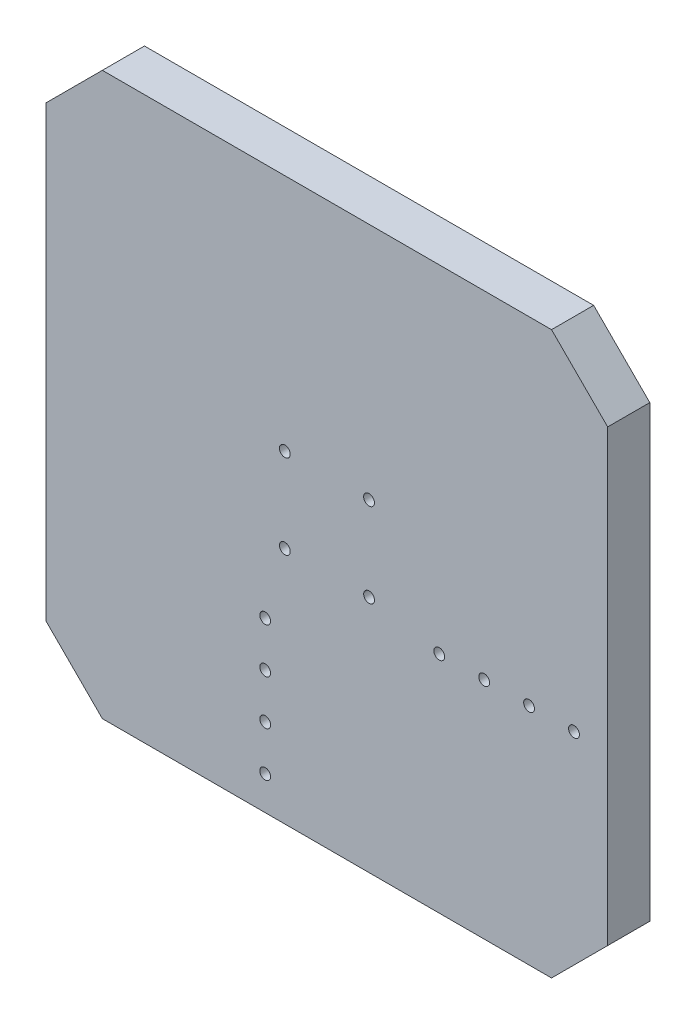
SolidWorks part; units mm, degrees
ref_plane "Front Plane" through (0, 0, 0) normal (0, 0, 1) x (1, 0, 0)
ref_plane "Top Plane" through (0, 0, 0) normal (0, 1, 0) x (1, 0, 0)
ref_plane "Right Plane" through (0, 0, 0) normal (1, 0, 0) x (0, 0, -1)
sketch "Sketch2" plane through (0, 0, 0) normal (0, 0, 1) x (1, 0, 0)
  line L1 (-100, -100) -> (100, -100)
  line L2 (-100, -100) -> (-100, 100)
  line L3 (-100, 100) -> (100, 100)
  line L4 (100, -100) -> (100, 100)
  line L5 (-100, -100) -> (100, 100) construction
  line L6 (-100, 100) -> (100, -100) construction
  point P0 (0, 0)
  dimension "D1" = 200
  dimension "D2" = 200
extrude "Boss-Extrude1" add sketch "Sketch2" along normal blind 15
chamfer "Chamfer1" distance 20 angle 45 4 edges at (-100, -100, 7.5) (-100, 100, 7.5) (100, 100, 7.5) (100, -100, 7.5)
sketch "Sketch3" plane through (0, 0, 15) normal (0, 0, 1) x (1, 0, 0)
  line L0 (0, 100) -> (0, -100) construction
  line L1 (80, 100) -> (-80, 100) construction
  line L2 (-80, -100) -> (80, -100) construction
  line L3 (100, 0) -> (-100, 0) construction
  line L4 (100, -80) -> (100, 80) construction
  line L5 (-100, 80) -> (-100, -80) construction
  circle A0 centre (-22, -88) radius 1.925
  circle A1 centre (-22, -72) radius 1.925
  circle A2 centre (-22, -56) radius 1.925
  circle A3 centre (-22, -40) radius 1.925
  circle A5 centre (-22, -24) radius 1.925 [skipped]
  dimension "D1" = 3.85
  dimension "D2" = 22
  dimension "D3" = 12
  dimension "D4" = 5
sketch "Sketch4" plane through (0, 0, 15) normal (0, 0, 1) x (1, 0, 0)
  line L0 (100, 0) -> (-100, 0) construction
  line L1 (100, -80) -> (100, 80) construction
  circle A0 centre (88, -20) radius 1.925
  circle A1 centre (72, -20) radius 1.925
  circle A2 centre (56, -20) radius 1.925
  circle A3 centre (40, -20) radius 1.925
  dimension "D1" = 3.85
  dimension "D3" = 12
  dimension "D2" = 20
  dimension "D4" = 4
extrude "Cut-Extrude1" cut sketch "Sketch3" against normal through all
extrude "Cut-Extrude2" cut sketch "Sketch4" against normal through all
sketch "Sketch5" plane through (0, 0, 15) normal (0, 0, 1) x (1, 0, 0)
  line L0 (0, 100) -> (0, -100) construction
  line L1 (80, 100) -> (-80, 100) construction
  line L2 (-80, -100) -> (80, -100) construction
  line L3 (100, 0) -> (-100, 0) construction
  line L4 (100, -80) -> (100, 80) construction
  line L5 (-100, 80) -> (-100, -80) construction
  circle A0 centre (15, 15) radius 1.925
  circle A1 centre (15, -15) radius 1.925
  circle A2 centre (-15, -15) radius 1.925
  circle A3 centre (-15, 15) radius 1.925
  dimension "D1" = 3.85
  dimension "D2" = 15
  dimension "D3" = 15
extrude "Cut-Extrude3" cut sketch "Sketch5" against normal through all
